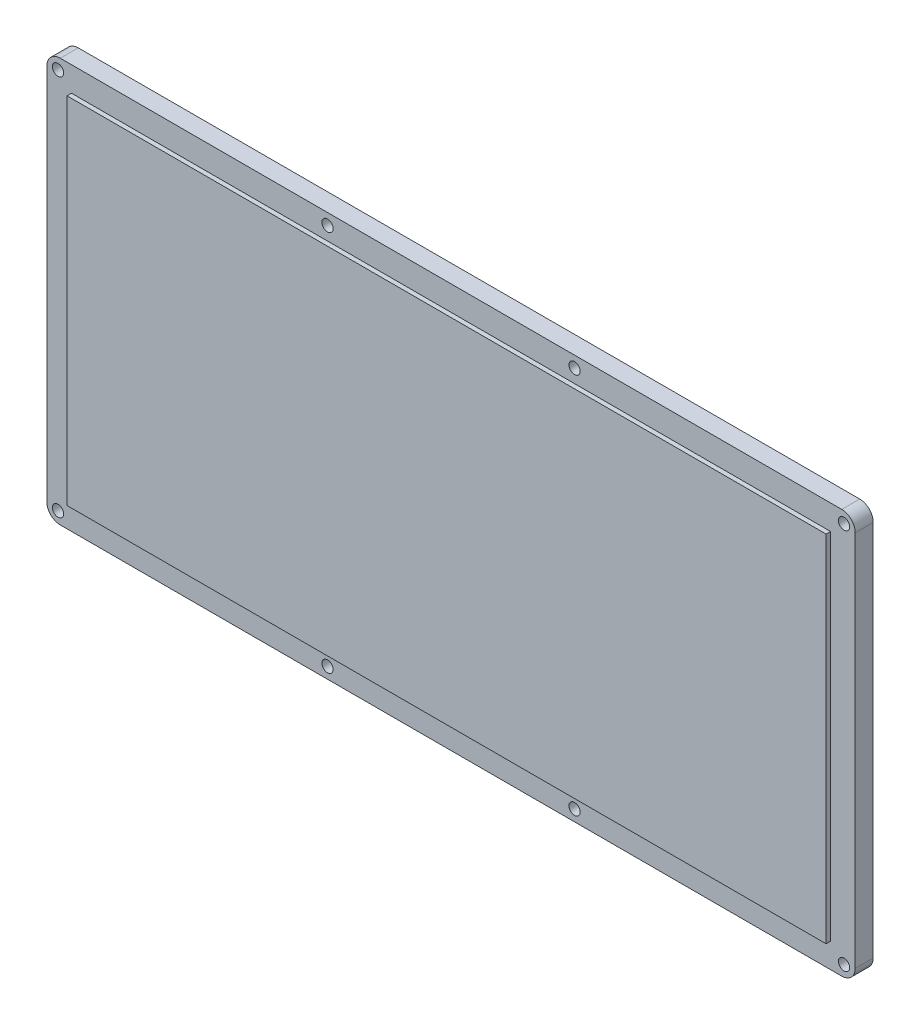
SolidWorks part; units mm, degrees
ref_plane "Front Plane" through (0, 0, 0) normal (0, 0, 1) x (1, 0, 0)
ref_plane "Top Plane" through (0, 0, 0) normal (0, 1, 0) x (1, 0, 0)
ref_plane "Right Plane" through (0, 0, 0) normal (1, 0, 0) x (0, 0, -1)
sketch "Sketch1" plane through (0, 0, 0) normal (0, 0, 1) x (1, 0, 0)
  line L1 (-90, 45) -> (90, 45)
  line L2 (-90, 45) -> (-90, -45)
  line L3 (-90, -45) -> (90, -45)
  line L4 (90, 45) -> (90, -45)
  point P4 (0, 45)
  point P6 (-90, 0)
  dimension "D1" = 180
  dimension "D2" = 90
extrude "Boss-Extrude1" add sketch "Sketch1" along normal blind 4
fillet "Fillet1" radius 3 4 edges at (90, 45, 2) (90, -45, 2) (-90, -45, 2) (-90, 45, 2)
sketch "Sketch2" plane through (0, 0, 4) normal (0, 0, 1) x (1, 0, 0)
  line L8 (84.5, -39.5) -> (84.5, 39.5)
  line L9 (84.5, 39.5) -> (-84.5, 39.5)
  line L10 (-84.5, 39.5) -> (-84.5, -39.5)
  line L11 (-84.5, -39.5) -> (84.5, -39.5)
  line L12 (84.5, -39.5) -> (84.5, 39.5)
  line L13 (84.5, 39.5) -> (-84.5, 39.5)
  line L14 (-84.5, 39.5) -> (-84.5, -39.5)
  line L15 (-84.5, -39.5) -> (84.5, -39.5)
  dimension "D1" = 5.5
extrude "Boss-Extrude2" add sketch "Sketch2" along normal blind 1
sketch "Sketch3" plane through (0, 0, 0) normal (0, 0, -1) x (-1, 0, 0)
  line L1 (-87.5, 42.5) -> (87.5, 42.5) construction
  line L2 (-87.5, 42.5) -> (-87.5, -42.5) construction
  line L3 (-87.5, -42.5) -> (87.5, -42.5) construction
  line L4 (87.5, 42.5) -> (87.5, -42.5) construction
  line L5 (-90, -42) -> (-90, 42) construction
  line L6 (-87, 45) -> (87, 45) construction
  circle A0 centre (-87.5, 42.5) radius 1.25
  circle A1 centre (87.5, 42.5) radius 1.25
  circle A2 centre (87.5, -42.5) radius 1.25
  circle A3 centre (-87.5, -42.5) radius 1.25
  circle A4 centre (-27.5, -42.5) radius 1.25
  circle A5 centre (27.5, 42.5) radius 1.25
  circle A6 centre (27.5, -42.5) radius 1.25
  circle A7 centre (-27.5, 42.5) radius 1.25
  point P4 (0, 42.5)
  point P6 (-87.5, 0)
  dimension "D1" = 2.5
  dimension "D4" = 2.5
  dimension "D5" = 2.5
  dimension "D6" = 60
  dimension "D7" = 2.5
  dimension "D8" = 60
  dimension "D9" = 60
  dimension "D10" = 2.5
  dimension "D2" = 2.5
  dimension "D3" = 2.5
  dimension "D11" = 60
extrude "Cut-Extrude2" cut sketch "Sketch3" against normal blind 10
sketch "Sketch4" plane through (0, 0, 0) normal (0, 0, -1) x (-1, 0, 0)
  line L0 (33.3333, 100) -> (166.6667, 100) construction
  line L1 (47.5892, 25.146) -> (-47.5892, 25.146)
  line L2 (-71.4139, 1.3212) -> (-71.4139, -1.3212)
  line L3 (-47.5892, -25.146) -> (47.5892, -25.146)
  line L4 (71.4139, -1.3212) -> (71.4139, 1.3212)
  line L5 (-27.9881, -11.6905) -> (-26.7934, -10.7431)
  line L6 (-13.3429, 2.4562) -> (-15.6911, 2.4562)
  line L7 (-5.6806, 7.8767) -> (-6.8547, 6.9073)
  line L8 (-15.6911, 4.0426) -> (-13.3429, 4.0426)
  line L9 (-13.3429, -0.717) -> (-15.6911, -0.717)
  line L10 (-3.3529, 9.8599) -> (-4.5065, 8.8684)
  line L11 (-15.6911, 0.8696) -> (-13.4254, 0.8696)
  line L12 (-25.6812, -9.7075) -> (-24.5277, -8.7158)
  line L13 (-15.6911, -2.3036) -> (-13.4254, -2.3036)
  line L14 (-23.3536, -7.7241) -> (-22.1795, -6.7547)
  line L15 (-13.3429, -3.8901) -> (-15.6911, -3.8901)
  line L16 (-1.046, 11.8431) -> (-2.2406, 10.8955)
  line L17 (24.3308, -5.2744) -> (25.4636, -6.2219)
  line L18 (25.4842, 6.7341) -> (24.3101, 5.828)
  line L19 (26.6583, -7.1282) -> (27.7706, -8.0963)
  line L20 (27.8118, 8.588) -> (26.6583, 7.6612)
  line L21 (28.9242, -9.0232) -> (30.0982, -9.9297)
  line L22 (30.1188, 10.4419) -> (28.9242, 9.5561)
  line L23 (55.4131, -5.2744) -> (56.5459, -6.2219)
  line L24 (56.5664, 6.7341) -> (55.3923, 5.828)
  line L25 (57.7405, -7.1282) -> (58.8529, -8.0963)
  line L26 (58.8941, 8.588) -> (57.7405, 7.6612)
  line L27 (60.0064, -9.0232) -> (61.1805, -9.9297)
  line L28 (61.201, 10.4419) -> (60.0064, 9.5561)
  spline S0 degree 3 poles (-35.6815, 4.87) (-36.3065, 6.3326) (-37.151, 7.5957) (-38.2151, 8.6602) knots 15 15 15 15 16 16 16 16
  spline S1 degree 3 poles (-35.6815, -4.3373) (-35.0569, -2.8747) (-34.7443, -1.3401) (-34.7443, 0.2666) (-34.7443, 1.8732) (-35.0569, 3.4076) (-35.6815, 4.87) knots 13 13 13 13 14 14 14 15 15 15 15
  spline S2 degree 3 poles (-38.2151, -8.1271) (-37.151, -7.0632) (-36.3065, -5.7996) (-35.6815, -4.3373) knots 12 12 12 12 13 13 13 13
  spline S3 degree 3 poles (-42.0051, -10.6608) (-40.5426, -10.0362) (-39.2794, -9.1916) (-38.2151, -8.1271) knots 11 11 11 11 12 12 12 12
  spline S4 degree 3 poles (-51.2124, -10.6608) (-49.7499, -11.2858) (-48.2153, -11.5979) (-46.6087, -11.5979) (-45.0021, -11.5979) (-43.4676, -11.2858) (-42.0051, -10.6608) knots 9 9 9 9 10 10 10 11 11 11 11
  spline S5 degree 3 poles (-55.0024, -8.1271) (-53.9384, -9.1916) (-52.6748, -10.0362) (-51.2124, -10.6608) knots 8 8 8 8 9 9 9 9
  spline S6 degree 3 poles (-57.536, -4.3373) (-56.9113, -5.7996) (-56.0668, -7.0632) (-55.0024, -8.1271) knots 7 7 7 7 8 8 8 8
  spline S7 degree 3 poles (-57.536, 4.87) (-58.161, 3.4076) (-58.4732, 1.8732) (-58.4732, 0.2666) (-58.4732, -1.3401) (-58.161, -2.8747) (-57.536, -4.3373) knots 5 5 5 5 6 6 6 7 7 7 7
  spline S8 degree 3 poles (-55.0024, 8.6602) (-56.0668, 7.5957) (-56.9113, 6.3326) (-57.536, 4.87) knots 4 4 4 4 5 5 5 5
  spline S9 degree 3 poles (-51.2124, 11.1937) (-52.6748, 10.5686) (-53.9384, 9.7242) (-55.0024, 8.6602) knots 3 3 3 3 4 4 4 4
  spline S10 degree 3 poles (-42.0051, 11.1937) (-43.4676, 11.8185) (-45.0021, 12.131) (-46.6087, 12.131) (-48.2153, 12.131) (-49.7499, 11.8185) (-51.2124, 11.1937) knots 1 1 1 1 2 2 2 3 3 3 3
  spline S11 degree 3 poles (-38.2151, 8.6602) (-39.2794, 9.7242) (-40.5426, 10.5686) (-42.0051, 11.1937) knots 0 0 0 0 1 1 1 1
  spline S12 degree 3 poles (-37.6177, 5.4777) (-36.6908, 3.8845) (-36.2274, 2.1477) (-36.2274, 0.2666) (-36.2274, -1.615) (-36.6908, -3.3521) (-37.6177, -4.9448) knots 10 10 10 10 11 11 11 12 12 12 12
  spline S13 degree 3 poles (-41.3974, 9.2574) (-39.8046, 8.3307) (-38.5446, 7.0706) (-37.6177, 5.4777) knots 9 9 9 9 10 10 10 10
  spline S14 degree 3 poles (-51.82, 9.2574) (-50.2272, 10.1844) (-48.4903, 10.6479) (-46.6087, 10.6479) (-44.7275, 10.6479) (-42.9906, 10.1844) (-41.3974, 9.2574) knots 7 7 7 7 8 8 8 9 9 9 9
  spline S15 degree 3 poles (-55.5998, 5.4777) (-54.6728, 7.0706) (-53.4132, 8.3307) (-51.82, 9.2574) knots 6 6 6 6 7 7 7 7
  spline S16 degree 3 poles (-55.5998, -4.9448) (-56.5267, -3.3521) (-56.9902, -1.615) (-56.9902, 0.2666) (-56.9902, 2.1477) (-56.5267, 3.8845) (-55.5998, 5.4777) knots 4 4 4 4 5 5 5 6 6 6 6
  spline S17 degree 3 poles (-51.82, -8.7246) (-53.4132, -7.7976) (-54.6728, -6.5379) (-55.5998, -4.9448) knots 3 3 3 3 4 4 4 4
  spline S18 degree 3 poles (-41.3974, -8.7246) (-42.9906, -9.6515) (-44.7275, -10.115) (-46.6087, -10.115) (-48.4903, -10.115) (-50.2272, -9.6515) (-51.82, -8.7246) knots 1 1 1 1 2 2 2 3 3 3 3
  spline S19 degree 3 poles (-37.6177, -4.9448) (-38.5446, -6.5379) (-39.8046, -7.7976) (-41.3974, -8.7246) knots 0 0 0 0 1 1 1 1
  spline S20 degree 3 poles (-40.3161, 6.5488) (-42.0534, 8.2926) (-44.1508, 9.1648) (-46.6087, 9.1648) knots 7 7 7 7 8 8 8 8
  spline S21 degree 3 poles (-40.3161, -6.0159) (-38.579, -4.2722) (-37.7104, -2.178) (-37.7104, 0.2666) (-37.7104, 2.7104) (-38.579, 4.8048) (-40.3161, 6.5488) knots 5 5 5 5 6 6 6 7 7 7 7
  spline S22 degree 3 poles (-52.9015, -6.0159) (-51.1644, -7.76) (-49.0669, -8.6319) (-46.6087, -8.6319) (-44.1508, -8.6319) (-42.0534, -7.76) (-40.3161, -6.0159) knots 3 3 3 3 4 4 4 5 5 5 5
  spline S23 degree 3 poles (-52.9015, 6.5488) (-54.6388, 4.8048) (-55.5071, 2.7104) (-55.5071, 0.2666) (-55.5071, -2.178) (-54.6388, -4.2722) (-52.9015, -6.0159) knots 1 1 1 1 2 2 2 3 3 3 3
  spline S24 degree 3 poles (-46.6087, 9.1648) (-49.0669, 9.1648) (-51.1644, 8.2926) (-52.9015, 6.5488) knots 0 0 0 0 1 1 1 1
  spline S25 degree 3 poles (-32.9523, 6.0236) (-33.735, 7.8567) (-34.7891, 9.4359) (-36.1141, 10.7612) knots 15 15 15 15 16 16 16 16
  spline S26 degree 3 poles (-32.9523, -5.4906) (-32.1696, -3.6575) (-31.7782, -1.7385) (-31.7782, 0.2666) (-31.7782, 2.2713) (-32.1696, 4.1904) (-32.9523, 6.0236) knots 13 13 13 13 14 14 14 15 15 15 15
  spline S27 degree 3 poles (-36.1141, -10.2282) (-34.7891, -8.9031) (-33.735, -7.324) (-32.9523, -5.4906) knots 12 12 12 12 13 13 13 13
  spline S28 degree 3 poles (-40.8516, -13.39) (-39.0184, -12.6074) (-37.4394, -11.5535) (-36.1141, -10.2282) knots 11 11 11 11 12 12 12 12
  spline S29 degree 3 poles (-52.3659, -13.39) (-50.5327, -14.1726) (-48.6138, -14.5641) (-46.6087, -14.5641) (-44.604, -14.5641) (-42.6848, -14.1726) (-40.8516, -13.39) knots 9 9 9 9 10 10 10 11 11 11 11
  spline S30 degree 3 poles (-57.1034, -10.2282) (-55.7784, -11.5535) (-54.1991, -12.6074) (-52.3659, -13.39) knots 8 8 8 8 9 9 9 9
  spline S31 degree 3 poles (-60.2652, -5.4906) (-59.4825, -7.324) (-58.4288, -8.9031) (-57.1034, -10.2282) knots 7 7 7 7 8 8 8 8
  spline S32 degree 3 poles (-60.2652, 6.0236) (-61.0479, 4.1904) (-61.4393, 2.2713) (-61.4393, 0.2666) (-61.4393, -1.7385) (-61.0479, -3.6575) (-60.2652, -5.4906) knots 5 5 5 5 6 6 6 7 7 7 7
  spline S33 degree 3 poles (-57.1034, 10.7612) (-58.4288, 9.4359) (-59.4825, 7.8567) (-60.2652, 6.0236) knots 4 4 4 4 5 5 5 5
  spline S34 degree 3 poles (-52.3659, 13.9229) (-54.1991, 13.1401) (-55.7784, 12.0861) (-57.1034, 10.7612) knots 3 3 3 3 4 4 4 4
  spline S35 degree 3 poles (-40.8516, 13.9229) (-42.6848, 14.7057) (-44.604, 15.097) (-46.6087, 15.097) (-48.6138, 15.097) (-50.5327, 14.7057) (-52.3659, 13.9229) knots 1 1 1 1 2 2 2 3 3 3 3
  spline S36 degree 3 poles (-36.1141, 10.7612) (-37.4394, 12.0861) (-39.0184, 13.1401) (-40.8516, 13.9229) knots 0 0 0 0 1 1 1 1
  spline S37 degree 3 poles (-34.322, 5.457) (-33.615, 3.8093) (-33.2613, 2.0792) (-33.2613, 0.2666) (-33.2613, -1.5461) (-33.615, -3.2764) (-34.322, -4.9243) knots 14 14 14 14 15 15 15 16 16 16 16
  spline S38 degree 3 poles (-37.1646, 9.7106) (-35.9769, 8.5228) (-35.0295, 7.1051) (-34.322, 5.457) knots 13 13 13 13 14 14 14 14
  spline S39 degree 3 poles (-41.418, 12.5531) (-39.7702, 11.8456) (-38.3525, 10.8983) (-37.1646, 9.7106) knots 12 12 12 12 13 13 13 13
  spline S40 degree 3 poles (-51.7994, 12.5531) (-50.1516, 13.2602) (-48.4214, 13.6139) (-46.6087, 13.6139) (-44.7961, 13.6139) (-43.0659, 13.2602) (-41.418, 12.5531) knots 10 10 10 10 11 11 11 12 12 12 12
  spline S41 degree 3 poles (-56.053, 9.7106) (-54.8653, 10.8983) (-53.4473, 11.8456) (-51.7994, 12.5531) knots 9 9 9 9 10 10 10 10
  spline S42 degree 3 poles (-58.8954, 5.457) (-58.1884, 7.1051) (-57.2409, 8.5228) (-56.053, 9.7106) knots 8 8 8 8 9 9 9 9
  spline S43 degree 3 poles (-58.8954, -4.9243) (-59.6029, -3.2764) (-59.9563, -1.5461) (-59.9563, 0.2666) (-59.9563, 2.0792) (-59.6029, 3.8093) (-58.8954, 5.457) knots 6 6 6 6 7 7 7 8 8 8 8
  spline S44 degree 3 poles (-56.053, -9.1777) (-57.2409, -7.99) (-58.1884, -6.572) (-58.8954, -4.9243) knots 5 5 5 5 6 6 6 6
  spline S45 degree 3 poles (-51.7994, -12.0203) (-53.4473, -11.3132) (-54.8653, -10.3657) (-56.053, -9.1777) knots 4 4 4 4 5 5 5 5
  spline S46 degree 3 poles (-41.418, -12.0203) (-43.0659, -12.7276) (-44.7961, -13.081) (-46.6087, -13.081) (-48.4214, -13.081) (-50.1516, -12.7276) (-51.7994, -12.0203) knots 2 2 2 2 3 3 3 4 4 4 4
  spline S47 degree 3 poles (-37.1646, -9.1777) (-38.3525, -10.3657) (-39.7702, -11.3132) (-41.418, -12.0203) knots 1 1 1 1 2 2 2 2
  spline S48 degree 3 poles (-34.322, -4.9243) (-35.0295, -6.572) (-35.9769, -7.99) (-37.1646, -9.1777) knots 0 0 0 0 1 1 1 1
  spline S49 degree 3 poles (-47.5892, 25.146) (-60.7472, 25.146) (-71.4139, 14.4793) (-71.4139, 1.3212) knots 1 1 1 1 2 2 2 2
  spline S50 degree 3 poles (-71.4139, -1.3212) (-71.4139, -14.4793) (-60.7472, -25.146) (-47.5892, -25.146) knots 3 3 3 3 4 4 4 4
  spline S51 degree 3 poles (47.5892, -25.146) (60.7472, -25.146) (71.4139, -14.4793) (71.4139, -1.3212) knots 5 5 5 5 6 6 6 6
  spline S52 degree 3 poles (71.4139, 1.3212) (71.4139, 14.4793) (60.7472, 25.146) (47.5892, 25.146) knots 7 7 7 7 8 8 8 8
  spline S53 degree 3 poles (-31.5928, 6.6003) (-30.7277, 4.5885) (-30.2952, 2.4773) (-30.2952, 0.2666) (-30.2952, -1.9445) (-30.7277, -4.0559) (-31.5928, -6.0674) knots 14 14 14 14 15 15 15 16 16 16 16
  spline S54 degree 3 poles (-35.0739, 11.8015) (-33.6185, 10.3457) (-32.4579, 8.6118) (-31.5928, 6.6003) knots 13 13 13 13 14 14 14 14
  spline S55 degree 3 poles (-40.2748, 15.2823) (-38.2633, 14.4172) (-36.5296, 13.2567) (-35.0739, 11.8015) knots 12 12 12 12 13 13 13 13
  spline S56 degree 3 poles (-52.9426, 15.2823) (-50.9311, 16.1474) (-48.8198, 16.5799) (-46.6087, 16.5799) (-44.398, 16.5799) (-42.2867, 16.1474) (-40.2748, 15.2823) knots 10 10 10 10 11 11 11 12 12 12 12
  spline S57 degree 3 poles (-58.1436, 11.8015) (-56.6882, 13.2567) (-54.9545, 14.4172) (-52.9426, 15.2823) knots 9 9 9 9 10 10 10 10
  spline S58 degree 3 poles (-61.6247, 6.6003) (-60.7596, 8.6118) (-59.5993, 10.3457) (-58.1436, 11.8015) knots 8 8 8 8 9 9 9 9
  spline S59 degree 3 poles (-61.6247, -6.0674) (-62.4897, -4.0559) (-62.9224, -1.9445) (-62.9224, 0.2666) (-62.9224, 2.4773) (-62.4897, 4.5885) (-61.6247, 6.6003) knots 6 6 6 6 7 7 7 8 8 8 8
  spline S60 degree 3 poles (-58.1436, -11.2684) (-59.5993, -9.8131) (-60.7596, -8.0793) (-61.6247, -6.0674) knots 5 5 5 5 6 6 6 6
  spline S61 degree 3 poles (-52.9426, -14.7496) (-54.9545, -13.8845) (-56.6882, -12.7241) (-58.1436, -11.2684) knots 4 4 4 4 5 5 5 5
  spline S62 degree 3 poles (-40.2748, -14.7496) (-42.2867, -15.6146) (-44.398, -16.0472) (-46.6087, -16.0472) (-48.8198, -16.0472) (-50.9311, -15.6146) (-52.9426, -14.7496) knots 2 2 2 2 3 3 3 4 4 4 4
  spline S63 degree 3 poles (-35.0739, -11.2684) (-36.5296, -12.7241) (-38.2633, -13.8845) (-40.2748, -14.7496) knots 1 1 1 1 2 2 2 2
  spline S64 degree 3 poles (-31.5928, -6.0674) (-32.4579, -8.0793) (-33.6185, -9.8131) (-35.0739, -11.2684) knots 0 0 0 0 1 1 1 1
  spline S65 degree 3 poles (-2.2818, -10.2141) (-2.8724, -11.4629) (-3.7206, -12.5609) (-4.8258, -13.5083) knots 0 0 0 0 1 1 1 1
  spline S66 degree 3 poles (-4.8258, -13.5083) (-5.9313, -14.456) (-7.3422, -15.205) (-9.0586, -15.756) knots 1 1 1 1 2 2 2 2
  spline S67 degree 3 poles (-9.0586, -15.756) (-10.7754, -16.3069) (-12.6839, -16.5824) (-14.7848, -16.5824) knots 2 2 2 2 3 3 3 3
  spline S68 degree 3 poles (-14.7848, -16.5824) (-17.4352, -16.5824) (-19.9137, -16.1526) (-22.2207, -15.2933) knots 3 3 3 3 4 4 4 4
  spline S69 degree 3 poles (-22.2207, -15.2933) (-24.5277, -14.4339) (-26.4504, -13.233) (-27.9881, -11.6905) knots 4 4 4 4 5 5 5 5
  spline S70 degree 3 poles (-26.7934, -10.7431) (-25.3928, -12.0948) (-23.6419, -13.1414) (-21.541, -13.8831) knots 6 6 6 6 7 7 7 7
  spline S71 degree 3 poles (-21.541, -13.8831) (-19.4399, -14.625) (-17.1881, -14.9958) (-14.7848, -14.9958) knots 7 7 7 7 8 8 8 8
  spline S72 degree 3 poles (-14.7848, -14.9958) (-11.0773, -14.9958) (-8.166, -14.1584) (-6.0513, -12.4838) knots 8 8 8 8 9 9 9 9
  spline S73 degree 3 poles (-6.0513, -12.4838) (-3.9368, -10.809) (-2.8791, -8.7158) (-2.8791, -6.2038) knots 9 9 9 9 10 10 10 10
  spline S74 degree 3 poles (-2.8791, -6.2038) (-2.8791, -3.5451) (-3.7855, -1.4369) (-5.5981, 0.1202) knots 10 10 10 10 11 11 11 11
  spline S75 degree 3 poles (-5.5981, 0.1202) (-7.4107, 1.6774) (-9.9926, 2.4562) (-13.3429, 2.4562) knots 11 11 11 11 12 12 12 12
  spline S76 degree 3 poles (-15.6911, 2.4562) (-19.701, 2.4562) (-21.7057, 3.7561) (-21.7057, 6.3563) knots 13 13 13 13 14 14 14 14
  spline S77 degree 3 poles (-21.7057, 6.3563) (-21.7057, 7.5314) (-21.0846, 8.4972) (-19.8416, 9.254) knots 14 14 14 14 15 15 15 15
  spline S78 degree 3 poles (-19.8416, 9.254) (-18.599, 10.0105) (-16.7349, 10.3887) (-14.2493, 10.3887) knots 15 15 15 15 16 16 16 16
  spline S79 degree 3 poles (-14.2493, 10.3887) (-12.5055, 10.3887) (-10.885, 10.1718) (-9.3881, 9.7387) knots 16 16 16 16 17 17 17 17
  spline S80 degree 3 poles (-9.3881, 9.7387) (-7.8916, 9.3052) (-6.6558, 8.6845) (-5.6806, 7.8767) knots 17 17 17 17 18 18 18 18
  spline S81 degree 3 poles (-6.8547, 6.9073) (-8.5713, 8.1704) (-11.036, 8.8021) (-14.2493, 8.8021) knots 19 19 19 19 20 20 20 20
  spline S82 degree 3 poles (-14.2493, 8.8021) (-16.3091, 8.8021) (-17.8198, 8.5743) (-18.7809, 8.119) knots 20 20 20 20 21 21 21 21
  spline S83 degree 3 poles (-18.7809, 8.119) (-19.7422, 7.6637) (-20.2227, 7.0759) (-20.2227, 6.3563) knots 21 21 21 21 22 22 22 22
  spline S84 degree 3 poles (-20.2227, 6.3563) (-20.2227, 5.5189) (-19.8864, 4.9239) (-19.2134, 4.5713) knots 22 22 22 22 23 23 23 23
  spline S85 degree 3 poles (-19.2134, 4.5713) (-18.5408, 4.2188) (-17.3667, 4.0426) (-15.6911, 4.0426) knots 23 23 23 23 24 24 24 24
  spline S86 degree 3 poles (-13.3429, 4.0426) (-9.5256, 4.0426) (-6.5801, 3.1132) (-4.5065, 1.2552) knots 25 25 25 25 26 26 26 26
  spline S87 degree 3 poles (-4.5065, 1.2552) (-2.4332, -0.6035) (-1.3962, -3.0896) (-1.3962, -6.2038) knots 26 26 26 26 27 27 27 27
  spline S88 degree 3 poles (-1.3962, -6.2038) (-1.3962, -7.6288) (-1.6917, -8.9657) (-2.2818, -10.2141) knots 27 27 27 27 28 28 28 28
  spline S89 degree 3 poles (-7.73, -2.1383) (-8.9866, -1.1909) (-10.8577, -0.717) (-13.3429, -0.717) knots 0 0 0 0 1 1 1 1
  spline S90 degree 3 poles (-15.6911, -0.717) (-18.5749, -0.717) (-20.7926, -0.089) (-22.3443, 1.167) knots 2 2 2 2 3 3 3 3
  spline S91 degree 3 poles (-22.3443, 1.167) (-23.8962, 2.423) (-24.6719, 4.1527) (-24.6719, 6.3563) knots 3 3 3 3 4 4 4 4
  spline S92 degree 3 poles (-24.6719, 6.3563) (-24.6719, 8.4127) (-23.7588, 10.1277) (-21.9324, 11.5014) knots 4 4 4 4 5 5 5 5
  spline S93 degree 3 poles (-21.9324, 11.5014) (-20.1062, 12.875) (-17.5449, 13.5618) (-14.2493, 13.5618) knots 5 5 5 5 6 6 6 6
  spline S94 degree 3 poles (-14.2493, 13.5618) (-12.0523, 13.5618) (-10.0028, 13.2385) (-8.1008, 12.5921) knots 6 6 6 6 7 7 7 7
  spline S95 degree 3 poles (-8.1008, 12.5921) (-6.1991, 11.9457) (-4.6164, 11.0349) (-3.3529, 9.8599) knots 7 7 7 7 8 8 8 8
  spline S96 degree 3 poles (-4.5065, 8.8684) (-5.6325, 9.8522) (-7.0471, 10.6163) (-8.7496, 11.16) knots 9 9 9 9 10 10 10 10
  spline S97 degree 3 poles (-8.7496, 11.16) (-10.4524, 11.7031) (-12.2858, 11.9753) (-14.2493, 11.9753) knots 10 10 10 10 11 11 11 11
  spline S98 degree 3 poles (-14.2493, 11.9753) (-17.1468, 11.9753) (-19.3611, 11.4463) (-20.8922, 10.3887) knots 11 11 11 11 12 12 12 12
  spline S99 degree 3 poles (-20.8922, 10.3887) (-22.4235, 9.3311) (-23.1889, 7.9868) (-23.1889, 6.3563) knots 12 12 12 12 13 13 13 13
  spline S100 degree 3 poles (-23.1889, 6.3563) (-23.1889, 4.5935) (-22.5606, 3.2383) (-21.3041, 2.2909) knots 13 13 13 13 14 14 14 14
  spline S101 degree 3 poles (-21.3041, 2.2909) (-20.0476, 1.3433) (-18.1768, 0.8696) (-15.6911, 0.8696) knots 14 14 14 14 15 15 15 15
  spline S102 degree 3 poles (-13.4254, 0.8696) (-10.5005, 0.8696) (-8.2588, 0.2416) (-6.7001, -1.0144) knots 16 16 16 16 17 17 17 17
  spline S103 degree 3 poles (-6.7001, -1.0144) (-5.1417, -2.2704) (-4.3622, -4.0003) (-4.3622, -6.2038) knots 17 17 17 17 18 18 18 18
  spline S104 degree 3 poles (-4.3622, -6.2038) (-4.3622, -8.2605) (-5.2757, -9.9755) (-7.1017, -11.349) knots 18 18 18 18 19 19 19 19
  spline S105 degree 3 poles (-7.1017, -11.349) (-8.9283, -12.7228) (-11.4891, -13.4092) (-14.7848, -13.4092) knots 19 19 19 19 20 20 20 20
  spline S106 degree 3 poles (-14.7848, -13.4092) (-16.9821, -13.4092) (-19.0316, -13.0863) (-20.9333, -12.4397) knots 20 20 20 20 21 21 21 21
  spline S107 degree 3 poles (-20.9333, -12.4397) (-22.8354, -11.7934) (-24.4179, -10.8827) (-25.6812, -9.7075) knots 21 21 21 21 22 22 22 22
  spline S108 degree 3 poles (-24.5277, -8.7158) (-23.4019, -9.7) (-21.9873, -10.4641) (-20.2845, -11.0074) knots 23 23 23 23 24 24 24 24
  spline S109 degree 3 poles (-20.2845, -11.0074) (-18.5819, -11.5511) (-16.7487, -11.8227) (-14.7848, -11.8227) knots 24 24 24 24 25 25 25 25
  spline S110 degree 3 poles (-14.7848, -11.8227) (-11.8875, -11.8227) (-9.6733, -11.2939) (-8.142, -10.2361) knots 25 25 25 25 26 26 26 26
  spline S111 degree 3 poles (-8.142, -10.2361) (-6.6109, -9.1785) (-5.8453, -7.8343) (-5.8453, -6.2038) knots 26 26 26 26 27 27 27 27
  spline S112 degree 3 poles (-5.8453, -6.2038) (-5.8453, -4.4409) (-6.4736, -3.0857) (-7.73, -2.1383) knots 27 27 27 27 28 28 28 28
  spline S113 degree 3 poles (-2.2406, 10.8955) (-3.6414, 12.247) (-5.3921, 13.2934) (-7.4932, 14.0355) knots 0 0 0 0 1 1 1 1
  spline S114 degree 3 poles (-7.4932, 14.0355) (-9.5941, 14.7773) (-11.8465, 15.1484) (-14.2493, 15.1484) knots 1 1 1 1 2 2 2 2
  spline S115 degree 3 poles (-14.2493, 15.1484) (-17.9569, 15.1484) (-20.8683, 14.311) (-22.9828, 12.6364) knots 2 2 2 2 3 3 3 3
  spline S116 degree 3 poles (-22.9828, 12.6364) (-25.0976, 10.9616) (-26.1549, 8.8684) (-26.1549, 6.3563) knots 3 3 3 3 4 4 4 4
  spline S117 degree 3 poles (-26.1549, 6.3563) (-26.1549, 3.6973) (-25.2486, 1.5892) (-23.436, 0.0322) knots 4 4 4 4 5 5 5 5
  spline S118 degree 3 poles (-23.436, 0.0322) (-21.6234, -1.5252) (-19.0419, -2.3036) (-15.6911, -2.3036) knots 5 5 5 5 6 6 6 6
  spline S119 degree 3 poles (-13.4254, -2.3036) (-9.3608, -2.3036) (-7.3284, -3.6035) (-7.3284, -6.2038) knots 7 7 7 7 8 8 8 8
  spline S120 degree 3 poles (-7.3284, -6.2038) (-7.3284, -7.3792) (-7.9497, -8.345) (-9.1924, -9.1014) knots 8 8 8 8 9 9 9 9
  spline S121 degree 3 poles (-9.1924, -9.1014) (-10.4354, -9.8582) (-12.2995, -10.2361) (-14.7848, -10.2361) knots 9 9 9 9 10 10 10 10
  spline S122 degree 3 poles (-14.7848, -10.2361) (-16.5289, -10.2361) (-18.1494, -10.0196) (-19.646, -9.5861) knots 10 10 10 10 11 11 11 11
  spline S123 degree 3 poles (-19.646, -9.5861) (-21.1429, -9.153) (-22.3787, -8.5322) (-23.3536, -7.7241) knots 11 11 11 11 12 12 12 12
  spline S124 degree 3 poles (-22.1795, -6.7547) (-20.4631, -8.0182) (-17.9981, -8.6497) (-14.7848, -8.6497) knots 13 13 13 13 14 14 14 14
  spline S125 degree 3 poles (-14.7848, -8.6497) (-12.7249, -8.6497) (-11.2147, -8.4221) (-10.2532, -7.9666) knots 14 14 14 14 15 15 15 15
  spline S126 degree 3 poles (-10.2532, -7.9666) (-9.2923, -7.5115) (-8.8114, -6.9237) (-8.8114, -6.2038) knots 15 15 15 15 16 16 16 16
  spline S127 degree 3 poles (-8.8114, -6.2038) (-8.8114, -5.3665) (-9.148, -4.7715) (-9.8207, -4.4189) knots 16 16 16 16 17 17 17 17
  spline S128 degree 3 poles (-9.8207, -4.4189) (-10.4937, -4.0662) (-11.6678, -3.8901) (-13.3429, -3.8901) knots 17 17 17 17 18 18 18 18
  spline S129 degree 3 poles (-15.6911, -3.8901) (-19.5089, -3.8901) (-22.4544, -2.9612) (-24.5277, -1.1027) knots 19 19 19 19 20 20 20 20
  spline S130 degree 3 poles (-24.5277, -1.1027) (-26.6013, 0.7557) (-27.638, 3.2416) (-27.638, 6.3563) knots 20 20 20 20 21 21 21 21
  spline S131 degree 3 poles (-27.638, 6.3563) (-27.638, 7.781) (-27.3429, 9.1178) (-26.7523, 10.3667) knots 21 21 21 21 22 22 22 22
  spline S132 degree 3 poles (-26.7523, 10.3667) (-26.162, 11.6151) (-25.314, 12.7134) (-24.2084, 13.6608) knots 22 22 22 22 23 23 23 23
  spline S133 degree 3 poles (-24.2084, 13.6608) (-23.1031, 14.6084) (-21.6923, 15.3576) (-19.9755, 15.9086) knots 23 23 23 23 24 24 24 24
  spline S134 degree 3 poles (-19.9755, 15.9086) (-18.2591, 16.4595) (-16.3503, 16.7348) (-14.2493, 16.7348) knots 24 24 24 24 25 25 25 25
  spline S135 degree 3 poles (-14.2493, 16.7348) (-11.5992, 16.7348) (-9.1204, 16.305) (-6.8134, 15.4458) knots 25 25 25 25 26 26 26 26
  spline S136 degree 3 poles (-6.8134, 15.4458) (-4.5065, 14.5863) (-2.584, 13.3854) (-1.046, 11.8431) knots 26 26 26 26 27 27 27 27
  spline S137 degree 3 poles (11.076, -6.0159) (12.8129, -7.76) (14.9104, -8.6319) (17.3685, -8.6319) knots 0 0 0 0 1 1 1 1
  spline S138 degree 3 poles (17.3685, -8.6319) (18.7417, -8.6319) (20.0393, -8.3331) (21.2616, -7.736) knots 1 1 1 1 2 2 2 2
  spline S139 degree 3 poles (21.2616, -7.736) (22.4837, -7.1385) (23.5068, -6.3181) (24.3308, -5.2744) knots 2 2 2 2 3 3 3 3
  spline S140 degree 3 poles (25.4636, -6.2219) (24.5023, -7.4305) (23.3143, -8.3815) (21.9001, -9.0747) knots 4 4 4 4 5 5 5 5
  spline S141 degree 3 poles (21.9001, -9.0747) (20.4856, -9.7682) (18.9752, -10.115) (17.3685, -10.115) knots 5 5 5 5 6 6 6 6
  spline S142 degree 3 poles (17.3685, -10.115) (15.4872, -10.115) (13.75, -9.6515) (12.1573, -8.7246) knots 6 6 6 6 7 7 7 7
  spline S143 degree 3 poles (12.1573, -8.7246) (10.5643, -7.7976) (9.3046, -6.5379) (8.3776, -4.9448) knots 7 7 7 7 8 8 8 8
  spline S144 degree 3 poles (8.3776, -4.9448) (7.4507, -3.3521) (6.9872, -1.615) (6.9872, 0.2666) knots 8 8 8 8 9 9 9 9
  spline S145 degree 3 poles (6.9872, 0.2666) (6.9872, 2.1477) (7.4507, 3.8845) (8.3776, 5.4777) knots 9 9 9 9 10 10 10 10
  spline S146 degree 3 poles (8.3776, 5.4777) (9.3046, 7.0706) (10.5643, 8.3307) (12.1573, 9.2574) knots 10 10 10 10 11 11 11 11
  spline S147 degree 3 poles (12.1573, 9.2574) (13.75, 10.1844) (15.4872, 10.6479) (17.3685, 10.6479) knots 11 11 11 11 12 12 12 12
  spline S148 degree 3 poles (17.3685, 10.6479) (18.9752, 10.6479) (20.4892, 10.301) (21.9104, 9.6076) knots 12 12 12 12 13 13 13 13
  spline S149 degree 3 poles (21.9104, 9.6076) (23.3317, 8.9141) (24.5229, 7.9562) (25.4842, 6.7341) knots 13 13 13 13 14 14 14 14
  spline S150 degree 3 poles (24.3101, 5.828) (23.4862, 6.8712) (22.4666, 7.6885) (21.2513, 8.2792) knots 15 15 15 15 16 16 16 16
  spline S151 degree 3 poles (21.2513, 8.2792) (20.036, 8.8694) (18.7417, 9.1648) (17.3685, 9.1648) knots 16 16 16 16 17 17 17 17
  spline S152 degree 3 poles (17.3685, 9.1648) (14.9104, 9.1648) (12.8129, 8.2926) (11.076, 6.5488) knots 17 17 17 17 18 18 18 18
  spline S153 degree 3 poles (11.076, 6.5488) (9.3387, 4.8048) (8.4703, 2.7104) (8.4703, 0.2666) knots 18 18 18 18 19 19 19 19
  spline S154 degree 3 poles (8.4703, 0.2666) (8.4703, -2.178) (9.3387, -4.2722) (11.076, -6.0159) knots 19 19 19 19 20 20 20 20
  spline S155 degree 3 poles (22.5594, 10.9362) (20.9388, 11.7325) (19.2087, 12.131) (17.3685, 12.131) knots 0 0 0 0 1 1 1 1
  spline S156 degree 3 poles (17.3685, 12.131) (15.7619, 12.131) (14.2275, 11.8185) (12.7649, 11.1937) knots 1 1 1 1 2 2 2 2
  spline S157 degree 3 poles (12.7649, 11.1937) (11.3025, 10.5686) (10.039, 9.7242) (8.9749, 8.6602) knots 2 2 2 2 3 3 3 3
  spline S158 degree 3 poles (8.9749, 8.6602) (7.9106, 7.5957) (7.066, 6.3326) (6.4414, 4.87) knots 3 3 3 3 4 4 4 4
  spline S159 degree 3 poles (6.4414, 4.87) (5.8164, 3.4076) (5.5041, 1.8732) (5.5041, 0.2666) knots 4 4 4 4 5 5 5 5
  spline S160 degree 3 poles (5.5041, 0.2666) (5.5041, -1.3401) (5.8164, -2.8747) (6.4414, -4.3373) knots 5 5 5 5 6 6 6 6
  spline S161 degree 3 poles (6.4414, -4.3373) (7.066, -5.7996) (7.9106, -7.0632) (8.9749, -8.1271) knots 6 6 6 6 7 7 7 7
  spline S162 degree 3 poles (8.9749, -8.1271) (10.039, -9.1916) (11.3025, -10.0362) (12.7649, -10.6608) knots 7 7 7 7 8 8 8 8
  spline S163 degree 3 poles (12.7649, -10.6608) (14.2275, -11.2858) (15.7619, -11.5979) (17.3685, -11.5979) knots 8 8 8 8 9 9 9 9
  spline S164 degree 3 poles (17.3685, -11.5979) (19.2087, -11.5979) (20.9388, -11.1998) (22.5594, -10.4033) knots 9 9 9 9 10 10 10 10
  spline S165 degree 3 poles (22.5594, -10.4033) (24.1794, -9.6071) (25.5459, -8.5155) (26.6583, -7.1282) knots 10 10 10 10 11 11 11 11
  spline S166 degree 3 poles (27.7706, -8.0963) (26.5208, -9.6482) (24.9899, -10.8668) (23.1772, -11.7524) knots 12 12 12 12 13 13 13 13
  spline S167 degree 3 poles (23.1772, -11.7524) (21.3646, -12.6382) (19.4284, -13.081) (17.3685, -13.081) knots 13 13 13 13 14 14 14 14
  spline S168 degree 3 poles (17.3685, -13.081) (15.5559, -13.081) (13.8257, -12.7276) (12.1779, -12.0203) knots 14 14 14 14 15 15 15 15
  spline S169 degree 3 poles (12.1779, -12.0203) (10.53, -11.3132) (9.112, -10.3657) (7.9245, -9.1777) knots 15 15 15 15 16 16 16 16
  spline S170 degree 3 poles (7.9245, -9.1777) (6.7365, -7.99) (5.7889, -6.572) (5.082, -4.9243) knots 16 16 16 16 17 17 17 17
  spline S171 degree 3 poles (5.082, -4.9243) (4.3745, -3.2764) (4.0212, -1.5461) (4.0212, 0.2666) knots 17 17 17 17 18 18 18 18
  spline S172 degree 3 poles (4.0212, 0.2666) (4.0212, 2.0792) (4.3745, 3.8093) (5.082, 5.457) knots 18 18 18 18 19 19 19 19
  spline S173 degree 3 poles (5.082, 5.457) (5.7889, 7.1051) (6.7365, 8.5228) (7.9245, 9.7106) knots 19 19 19 19 20 20 20 20
  spline S174 degree 3 poles (7.9245, 9.7106) (9.112, 10.8983) (10.53, 11.8456) (12.1779, 12.5531) knots 20 20 20 20 21 21 21 21
  spline S175 degree 3 poles (12.1779, 12.5531) (13.8257, 13.2602) (15.5559, 13.6139) (17.3685, 13.6139) knots 21 21 21 21 22 22 22 22
  spline S176 degree 3 poles (17.3685, 13.6139) (19.442, 13.6139) (21.3884, 13.1676) (23.2082, 12.2751) knots 22 22 22 22 23 23 23 23
  spline S177 degree 3 poles (23.2082, 12.2751) (25.0274, 11.3823) (26.562, 10.1534) (27.8118, 8.588) knots 23 23 23 23 24 24 24 24
  spline S178 degree 3 poles (26.6583, 7.6612) (25.5459, 9.0479) (24.1794, 10.1397) (22.5594, 10.9362) knots 25 25 25 25 26 26 26 26
  spline S179 degree 3 poles (23.826, 13.6139) (21.8142, 14.6027) (19.6617, 15.097) (17.3685, 15.097) knots 0 0 0 0 1 1 1 1
  spline S180 degree 3 poles (17.3685, 15.097) (15.3635, 15.097) (13.4447, 14.7057) (11.6115, 13.9229) knots 1 1 1 1 2 2 2 2
  spline S181 degree 3 poles (11.6115, 13.9229) (9.7782, 13.1401) (8.199, 12.0861) (6.8739, 10.7612) knots 2 2 2 2 3 3 3 3
  spline S182 degree 3 poles (6.8739, 10.7612) (5.5486, 9.4359) (4.4949, 7.8567) (3.7122, 6.0236) knots 3 3 3 3 4 4 4 4
  spline S183 degree 3 poles (3.7122, 6.0236) (2.9294, 4.1904) (2.5381, 2.2713) (2.5381, 0.2666) knots 4 4 4 4 5 5 5 5
  spline S184 degree 3 poles (2.5381, 0.2666) (2.5381, -1.7385) (2.9294, -3.6575) (3.7122, -5.4906) knots 5 5 5 5 6 6 6 6
  spline S185 degree 3 poles (3.7122, -5.4906) (4.4949, -7.324) (5.5486, -8.9031) (6.8739, -10.2282) knots 6 6 6 6 7 7 7 7
  spline S186 degree 3 poles (6.8739, -10.2282) (8.199, -11.5535) (9.7782, -12.6074) (11.6115, -13.39) knots 7 7 7 7 8 8 8 8
  spline S187 degree 3 poles (11.6115, -13.39) (13.4447, -14.1726) (15.3635, -14.5641) (17.3685, -14.5641) knots 8 8 8 8 9 9 9 9
  spline S188 degree 3 poles (17.3685, -14.5641) (19.6617, -14.5641) (21.8142, -14.0698) (23.826, -13.081) knots 9 9 9 9 10 10 10 10
  spline S189 degree 3 poles (23.826, -13.081) (25.8375, -12.0924) (27.5369, -10.7399) (28.9242, -9.0232) knots 10 10 10 10 11 11 11 11
  spline S190 degree 3 poles (30.0982, -9.9297) (28.5739, -11.8244) (26.7026, -13.318) (24.4853, -14.4096) knots 12 12 12 12 13 13 13 13
  spline S191 degree 3 poles (24.4853, -14.4096) (22.2674, -15.5012) (19.8951, -16.0472) (17.3685, -16.0472) knots 13 13 13 13 14 14 14 14
  spline S192 degree 3 poles (17.3685, -16.0472) (15.1575, -16.0472) (13.0463, -15.6146) (11.0347, -14.7496) knots 14 14 14 14 15 15 15 15
  spline S193 degree 3 poles (11.0347, -14.7496) (9.0229, -13.8845) (7.2891, -12.7241) (5.8338, -11.2684) knots 15 15 15 15 16 16 16 16
  spline S194 degree 3 poles (5.8338, -11.2684) (4.378, -9.8131) (3.2179, -8.0793) (2.3526, -6.0674) knots 16 16 16 16 17 17 17 17
  spline S195 degree 3 poles (2.3526, -6.0674) (1.4875, -4.0559) (1.055, -1.9445) (1.055, 0.2666) knots 17 17 17 17 18 18 18 18
  spline S196 degree 3 poles (1.055, 0.2666) (1.055, 2.4773) (1.4875, 4.5885) (2.3526, 6.6003) knots 18 18 18 18 19 19 19 19
  spline S197 degree 3 poles (2.3526, 6.6003) (3.2179, 8.6118) (4.378, 10.3457) (5.8338, 11.8015) knots 19 19 19 19 20 20 20 20
  spline S198 degree 3 poles (5.8338, 11.8015) (7.2891, 13.2567) (9.0229, 14.4172) (11.0347, 15.2823) knots 20 20 20 20 21 21 21 21
  spline S199 degree 3 poles (11.0347, 15.2823) (13.0463, 16.1474) (15.1575, 16.5799) (17.3685, 16.5799) knots 21 21 21 21 22 22 22 22
  spline S200 degree 3 poles (17.3685, 16.5799) (19.8951, 16.5799) (22.2709, 16.0343) (24.4956, 14.9425) knots 22 22 22 22 23 23 23 23
  spline S201 degree 3 poles (24.4956, 14.9425) (26.72, 13.8507) (28.5944, 12.3504) (30.1188, 10.4419) knots 23 23 23 23 24 24 24 24
  spline S202 degree 3 poles (28.9242, 9.5561) (27.5369, 11.2725) (25.8375, 12.6251) (23.826, 13.6139) knots 25 25 25 25 26 26 26 26
  spline S203 degree 3 poles (42.1582, -6.0159) (43.8952, -7.76) (45.9927, -8.6319) (48.4508, -8.6319) knots 0 0 0 0 1 1 1 1
  spline S204 degree 3 poles (48.4508, -8.6319) (49.8239, -8.6319) (51.1216, -8.3331) (52.3439, -7.736) knots 1 1 1 1 2 2 2 2
  spline S205 degree 3 poles (52.3439, -7.736) (53.566, -7.1385) (54.589, -6.3181) (55.4131, -5.2744) knots 2 2 2 2 3 3 3 3
  spline S206 degree 3 poles (56.5459, -6.2219) (55.5846, -7.4305) (54.3966, -8.3815) (52.9824, -9.0747) knots 4 4 4 4 5 5 5 5
  spline S207 degree 3 poles (52.9824, -9.0747) (51.5679, -9.7682) (50.0574, -10.115) (48.4508, -10.115) knots 5 5 5 5 6 6 6 6
  spline S208 degree 3 poles (48.4508, -10.115) (46.5694, -10.115) (44.8323, -9.6515) (43.2396, -8.7246) knots 6 6 6 6 7 7 7 7
  spline S209 degree 3 poles (43.2396, -8.7246) (41.6465, -7.7976) (40.3868, -6.5379) (39.4598, -4.9448) knots 7 7 7 7 8 8 8 8
  spline S210 degree 3 poles (39.4598, -4.9448) (38.533, -3.3521) (38.0695, -1.615) (38.0695, 0.2666) knots 8 8 8 8 9 9 9 9
  spline S211 degree 3 poles (38.0695, 0.2666) (38.0695, 2.1477) (38.533, 3.8845) (39.4598, 5.4777) knots 9 9 9 9 10 10 10 10
  spline S212 degree 3 poles (39.4598, 5.4777) (40.3868, 7.0706) (41.6465, 8.3307) (43.2396, 9.2574) knots 10 10 10 10 11 11 11 11
  spline S213 degree 3 poles (43.2396, 9.2574) (44.8323, 10.1844) (46.5694, 10.6479) (48.4508, 10.6479) knots 11 11 11 11 12 12 12 12
  spline S214 degree 3 poles (48.4508, 10.6479) (50.0574, 10.6479) (51.5715, 10.301) (52.9927, 9.6076) knots 12 12 12 12 13 13 13 13
  spline S215 degree 3 poles (52.9927, 9.6076) (54.414, 8.9141) (55.6051, 7.9562) (56.5664, 6.7341) knots 13 13 13 13 14 14 14 14
  spline S216 degree 3 poles (55.3923, 5.828) (54.5685, 6.8712) (53.5489, 7.6885) (52.3336, 8.2792) knots 15 15 15 15 16 16 16 16
  spline S217 degree 3 poles (52.3336, 8.2792) (51.1183, 8.8694) (49.8239, 9.1648) (48.4508, 9.1648) knots 16 16 16 16 17 17 17 17
  spline S218 degree 3 poles (48.4508, 9.1648) (45.9927, 9.1648) (43.8952, 8.2926) (42.1582, 6.5488) knots 17 17 17 17 18 18 18 18
  spline S219 degree 3 poles (42.1582, 6.5488) (40.4209, 4.8048) (39.5526, 2.7104) (39.5526, 0.2666) knots 18 18 18 18 19 19 19 19
  spline S220 degree 3 poles (39.5526, 0.2666) (39.5526, -2.178) (40.4209, -4.2722) (42.1582, -6.0159) knots 19 19 19 19 20 20 20 20
  spline S221 degree 3 poles (53.6416, 10.9362) (52.0211, 11.7325) (50.2909, 12.131) (48.4508, 12.131) knots 0 0 0 0 1 1 1 1
  spline S222 degree 3 poles (48.4508, 12.131) (46.8442, 12.131) (45.3097, 11.8185) (43.8472, 11.1937) knots 1 1 1 1 2 2 2 2
  spline S223 degree 3 poles (43.8472, 11.1937) (42.3848, 10.5686) (41.1213, 9.7242) (40.0571, 8.6602) knots 2 2 2 2 3 3 3 3
  spline S224 degree 3 poles (40.0571, 8.6602) (38.9928, 7.5957) (38.1483, 6.3326) (37.5236, 4.87) knots 3 3 3 3 4 4 4 4
  spline S225 degree 3 poles (37.5236, 4.87) (36.8987, 3.4076) (36.5864, 1.8732) (36.5864, 0.2666) knots 4 4 4 4 5 5 5 5
  spline S226 degree 3 poles (36.5864, 0.2666) (36.5864, -1.3401) (36.8987, -2.8747) (37.5236, -4.3373) knots 5 5 5 5 6 6 6 6
  spline S227 degree 3 poles (37.5236, -4.3373) (38.1483, -5.7996) (38.9928, -7.0632) (40.0571, -8.1271) knots 6 6 6 6 7 7 7 7
  spline S228 degree 3 poles (40.0571, -8.1271) (41.1213, -9.1916) (42.3848, -10.0362) (43.8472, -10.6608) knots 7 7 7 7 8 8 8 8
  spline S229 degree 3 poles (43.8472, -10.6608) (45.3097, -11.2858) (46.8442, -11.5979) (48.4508, -11.5979) knots 8 8 8 8 9 9 9 9
  spline S230 degree 3 poles (48.4508, -11.5979) (50.2909, -11.5979) (52.0211, -11.1998) (53.6416, -10.4033) knots 9 9 9 9 10 10 10 10
  spline S231 degree 3 poles (53.6416, -10.4033) (55.2617, -9.6071) (56.6282, -8.5155) (57.7405, -7.1282) knots 10 10 10 10 11 11 11 11
  spline S232 degree 3 poles (58.8529, -8.0963) (57.6031, -9.6482) (56.0721, -10.8668) (54.2595, -11.7524) knots 12 12 12 12 13 13 13 13
  spline S233 degree 3 poles (54.2595, -11.7524) (52.4469, -12.6382) (50.5107, -13.081) (48.4508, -13.081) knots 13 13 13 13 14 14 14 14
  spline S234 degree 3 poles (48.4508, -13.081) (46.6382, -13.081) (44.908, -12.7276) (43.2601, -12.0203) knots 14 14 14 14 15 15 15 15
  spline S235 degree 3 poles (43.2601, -12.0203) (41.6123, -11.3132) (40.1942, -10.3657) (39.0068, -9.1777) knots 15 15 15 15 16 16 16 16
  spline S236 degree 3 poles (39.0068, -9.1777) (37.8187, -7.99) (36.8712, -6.572) (36.1642, -4.9243) knots 16 16 16 16 17 17 17 17
  spline S237 degree 3 poles (36.1642, -4.9243) (35.4568, -3.2764) (35.1034, -1.5461) (35.1034, 0.2666) knots 17 17 17 17 18 18 18 18
  spline S238 degree 3 poles (35.1034, 0.2666) (35.1034, 2.0792) (35.4568, 3.8093) (36.1642, 5.457) knots 18 18 18 18 19 19 19 19
  spline S239 degree 3 poles (36.1642, 5.457) (36.8712, 7.1051) (37.8187, 8.5228) (39.0068, 9.7106) knots 19 19 19 19 20 20 20 20
  spline S240 degree 3 poles (39.0068, 9.7106) (40.1942, 10.8983) (41.6123, 11.8456) (43.2601, 12.5531) knots 20 20 20 20 21 21 21 21
  spline S241 degree 3 poles (43.2601, 12.5531) (44.908, 13.2602) (46.6382, 13.6139) (48.4508, 13.6139) knots 21 21 21 21 22 22 22 22
  spline S242 degree 3 poles (48.4508, 13.6139) (50.5243, 13.6139) (52.4707, 13.1676) (54.2905, 12.2751) knots 22 22 22 22 23 23 23 23
  spline S243 degree 3 poles (54.2905, 12.2751) (56.1097, 11.3823) (57.6443, 10.1534) (58.8941, 8.588) knots 23 23 23 23 24 24 24 24
  spline S244 degree 3 poles (57.7405, 7.6612) (56.6282, 9.0479) (55.2617, 10.1397) (53.6416, 10.9362) knots 25 25 25 25 26 26 26 26
  spline S245 degree 3 poles (54.9083, 13.6139) (52.8964, 14.6027) (50.744, 15.097) (48.4508, 15.097) knots 0 0 0 0 1 1 1 1
  spline S246 degree 3 poles (48.4508, 15.097) (46.4457, 15.097) (44.527, 14.7057) (42.6938, 13.9229) knots 1 1 1 1 2 2 2 2
  spline S247 degree 3 poles (42.6938, 13.9229) (40.8604, 13.1401) (39.2813, 12.0861) (37.9562, 10.7612) knots 2 2 2 2 3 3 3 3
  spline S248 degree 3 poles (37.9562, 10.7612) (36.6309, 9.4359) (35.5772, 7.8567) (34.7944, 6.0236) knots 3 3 3 3 4 4 4 4
  spline S249 degree 3 poles (34.7944, 6.0236) (34.0116, 4.1904) (33.6203, 2.2713) (33.6203, 0.2666) knots 4 4 4 4 5 5 5 5
  spline S250 degree 3 poles (33.6203, 0.2666) (33.6203, -1.7385) (34.0116, -3.6575) (34.7944, -5.4906) knots 5 5 5 5 6 6 6 6
  spline S251 degree 3 poles (34.7944, -5.4906) (35.5772, -7.324) (36.6309, -8.9031) (37.9562, -10.2282) knots 6 6 6 6 7 7 7 7
  spline S252 degree 3 poles (37.9562, -10.2282) (39.2813, -11.5535) (40.8604, -12.6074) (42.6938, -13.39) knots 7 7 7 7 8 8 8 8
  spline S253 degree 3 poles (42.6938, -13.39) (44.527, -14.1726) (46.4457, -14.5641) (48.4508, -14.5641) knots 8 8 8 8 9 9 9 9
  spline S254 degree 3 poles (48.4508, -14.5641) (50.744, -14.5641) (52.8964, -14.0698) (54.9083, -13.081) knots 9 9 9 9 10 10 10 10
  spline S255 degree 3 poles (54.9083, -13.081) (56.9198, -12.0924) (58.6192, -10.7399) (60.0064, -9.0232) knots 10 10 10 10 11 11 11 11
  spline S256 degree 3 poles (61.1805, -9.9297) (59.6562, -11.8244) (57.7849, -13.318) (55.5676, -14.4096) knots 12 12 12 12 13 13 13 13
  spline S257 degree 3 poles (55.5676, -14.4096) (53.3497, -15.5012) (50.9773, -16.0472) (48.4508, -16.0472) knots 13 13 13 13 14 14 14 14
  spline S258 degree 3 poles (48.4508, -16.0472) (46.2397, -16.0472) (44.1285, -15.6146) (42.117, -14.7496) knots 14 14 14 14 15 15 15 15
  spline S259 degree 3 poles (42.117, -14.7496) (40.1052, -13.8845) (38.3713, -12.7241) (36.9161, -11.2684) knots 15 15 15 15 16 16 16 16
  spline S260 degree 3 poles (36.9161, -11.2684) (35.4603, -9.8131) (34.3001, -8.0793) (33.4349, -6.0674) knots 16 16 16 16 17 17 17 17
  spline S261 degree 3 poles (33.4349, -6.0674) (32.5698, -4.0559) (32.1372, -1.9445) (32.1372, 0.2666) knots 17 17 17 17 18 18 18 18
  spline S262 degree 3 poles (32.1372, 0.2666) (32.1372, 2.4773) (32.5698, 4.5885) (33.4349, 6.6003) knots 18 18 18 18 19 19 19 19
  spline S263 degree 3 poles (33.4349, 6.6003) (34.3001, 8.6118) (35.4603, 10.3457) (36.9161, 11.8015) knots 19 19 19 19 20 20 20 20
  spline S264 degree 3 poles (36.9161, 11.8015) (38.3713, 13.2567) (40.1052, 14.4172) (42.117, 15.2823) knots 20 20 20 20 21 21 21 21
  spline S265 degree 3 poles (42.117, 15.2823) (44.1285, 16.1474) (46.2397, 16.5799) (48.4508, 16.5799) knots 21 21 21 21 22 22 22 22
  spline S266 degree 3 poles (48.4508, 16.5799) (50.9773, 16.5799) (53.3532, 16.0343) (55.5778, 14.9425) knots 22 22 22 22 23 23 23 23
  spline S267 degree 3 poles (55.5778, 14.9425) (57.8023, 13.8507) (59.6767, 12.3504) (61.201, 10.4419) knots 23 23 23 23 24 24 24 24
  spline S268 degree 3 poles (60.0064, 9.5561) (58.6192, 11.2725) (56.9198, 12.6251) (54.9083, 13.6139) knots 25 25 25 25 26 26 26 26
  point P299 (0, 0)
  point P300 (0, 25.146)
  point P301 (71.4139, 0)
extrude "Boss-Extrude4" add sketch "Sketch4" along normal blind 1 contours S202 L22 S201 S200 S199 S198 S197 S196 S195 S194 S193 S192 S191 S190 L21 S189 S188 S187 S186 S185 S184 S183 S182 S181 S180 S179 | S178 L20 S177 S176 S175 S174 S173 S172 S171 S170 S169 S168 S167 S166 L19 S165 S164 S163 S162 S161 S160 S159 S158 S157 S156 S155 | S154 S153 S152 S151 S150 L18 S149 S148 S147 S146 S145 S144 S143 S142 S141 S140 L17 S139 S138 S137 | S244 L26 S243 S242 S241 S240 S239 S238 S237 S236 S235 S234 S233 S232 L25 S231 S230 S229 S228 S227 S226 S225 S224 S223 S222 S221 | S136 L16 S113 S114 S115 S116 S117 S118 L13 S119 S120 S121 S122 S123 L14 S124 S125 S126 S127 S128 L15 S129 S130 S131 S132 S133 S134 S135 | S50 L3 S51 L4 S52 L1 S49 L2 | S22 S21 S20 S24 S23 | S62 S61 S60 S59 S58 S57 S56 S55 S54 S53 S64 S63 | S4 S3 S2 S1 S0 S11 S10 S9 S8 S7 S6 S5 | S29 S28 S27 S26 S25 S36 S35 S34 S33 S32 S31 S30 | S46 S45 S44 S43 S42 S41 S40 S39 S38 S37 S48 S47 | S18 S17 S16 S15 S14 S13 S12 S19 | S68 S69 L5 S70 S71 S72 S73 S74 S75 L6 S76 S77 S78 S79 S80 L7 S81 S82 S83 S84 S85 L8 S86 S87 S88 S65 S66 S67 | S106 S107 L12 S108 S109 S110 S111 S112 S89 L9 S90 S91 S92 S93 S94 S95 L10 S96 S97 S98 S99 S100 S101 L11 S102 S103 S104 S105 | S252 S253 S254 S255 L27 S256 S257 S258 S259 S260 S261 S262 S263 S264 S265 S266 S267 L28 S268 S245 S246 S247 S248 S249 S250 S251 | S203 S204 S205 L23 S206 S207 S208 S209 S210 S211 S212 S213 S214 S215 L24 S216 S217 S218 S219 S220
